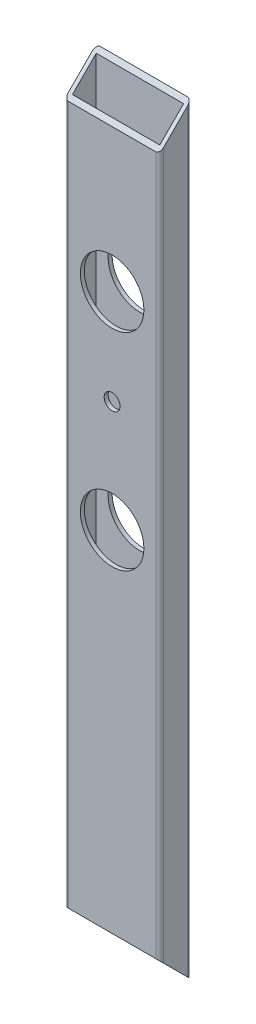
SolidWorks part; units mm, degrees
ref_plane "Front Plane" through (0, 0, 0) normal (0, 0, 1) x (1, 0, 0)
ref_plane "Top Plane" through (0, 0, 0) normal (0, 1, 0) x (1, 0, 0)
ref_plane "Right Plane" through (0, 0, 0) normal (1, 0, 0) x (0, 0, -1)
sketch "Sketch1" plane through (0, 0, 0) normal (0, 1, 0) x (1, 0, 0)
  line L0 (1.5875, 1.5875) -> (0, 1.5875) construction
  line L1 (1.5875, 0) -> (36.5125, 0)
  line L2 (0, 1.5875) -> (0, 11.1125)
  line L3 (1.5875, 12.7) -> (36.5125, 12.7)
  line L4 (38.1, 1.5875) -> (38.1, 11.1125)
  line L5 (1.5875, 1.5875) -> (36.5125, 1.5875)
  line L6 (1.5875, 1.5875) -> (1.5875, 11.1125)
  line L7 (1.5875, 11.1125) -> (36.5125, 11.1125)
  line L8 (36.5125, 1.5875) -> (36.5125, 11.1125)
  line L9 (1.5875, 1.5875) -> (1.5875, 0) construction
  line L10 (36.5125, 11.1125) -> (36.5125, 12.7) construction
  line L11 (36.5125, 11.1125) -> (38.1, 11.1125) construction
  arc A0 (1.5875, 0) -> (0, 1.5875) centre (1.5875, 1.5875) cw
  arc A1 (36.5125, 0) -> (38.1, 1.5875) centre (36.5125, 1.5875) ccw
  arc A2 (36.5125, 12.7) -> (38.1, 11.1125) centre (36.5125, 11.1125) cw
  arc A3 (0, 11.1125) -> (1.5875, 12.7) centre (1.5875, 11.1125) cw
  point P16 (0, 0)
  point P19 (38.1, 0)
  point P22 (38.1, 12.7)
  point P25 (0, 12.7)
  dimension "D4" = 1.5875
  dimension "D1" = 38.1
  dimension "D2" = 12.7
  dimension "D3" = 1.5875
extrude "Boss-Extrude1" add sketch "Sketch1" along normal blind 304.8
sketch "Sketch2" plane through (0, 0, 0) normal (0, 0, 1) x (1, 0, 0)
  line L0 (19.05, 0) -> (19.05, 304.8) construction
  line L1 (1.5875, 0) -> (36.5125, 0) construction
  line L2 (1.5875, 304.8) -> (36.5125, 304.8) construction
  line L3 (38.1, 304.8) -> (38.1, 0) construction
  circle A0 centre (19.05, 152.4) radius 12.7
  circle A1 centre (19.05, 196.85) radius 3.175
  circle A2 centre (19.05, 234.95) radius 12.7
  dimension "D1" = 25.4
  dimension "D2" = 25.4
  dimension "D3" = 6.35
  dimension "D4" = 19.05
  dimension "D5" = 152.4
  dimension "D6" = 44.45
  dimension "D7" = 38.1
extrude "Cut-Extrude1" cut sketch "Sketch2" against normal through all
sketch "Sketch3" plane through (38.1, 0, 0) normal (1, 0, 0) x (0, 0, -1)
  line L0 (0, 0) -> (12.7, 0)
  line L1 (12.7, 0) -> (0, 12.7)
  line L2 (0, 304.8) -> (0, 0) construction
  line L3 (0, 12.7) -> (0, 0)
  line L4 (0, 304.8) -> (12.7, 304.8)
  line L5 (12.7, 304.8) -> (0, 292.1)
  line L6 (0, 292.1) -> (0, 304.8)
extrude "Cut-Extrude2" cut sketch "Sketch3" against normal through all
